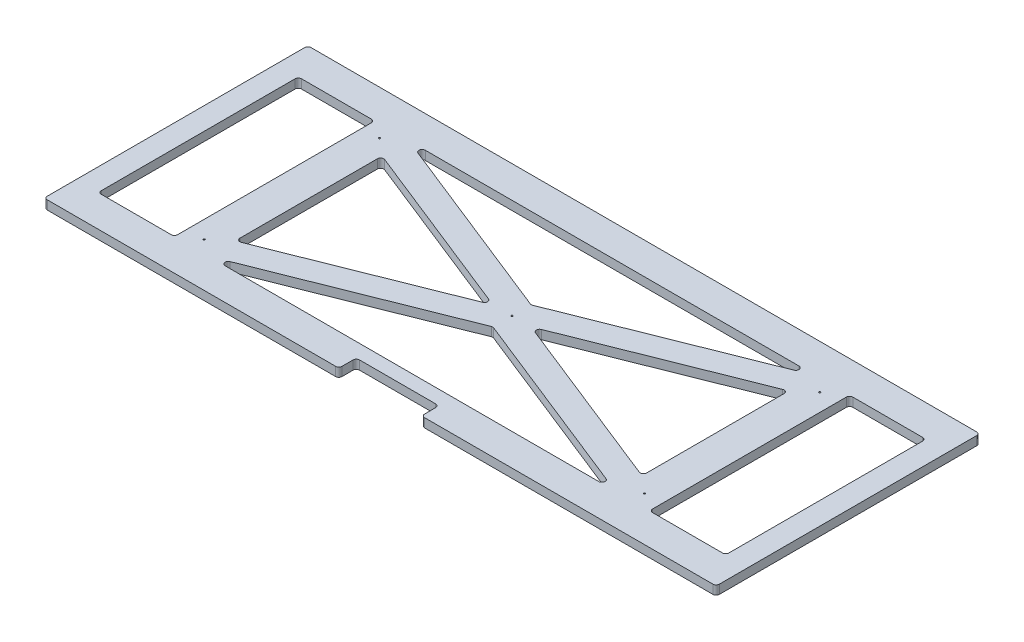
SolidWorks part; units mm, degrees
ref_plane "Front Plane" through (0, 0, 0) normal (0, 0, 1) x (1, 0, 0)
ref_plane "Top Plane" through (0, 0, 0) normal (0, 1, 0) x (1, 0, 0)
ref_plane "Right Plane" through (0, 0, 0) normal (1, 0, 0) x (0, 0, -1)
sketch "Sketch1" plane through (0, 0, 0) normal (0, 1, 0) x (1, 0, 0)
  line L1 (-671.5125, 263.525) -> (671.5125, 263.525)
  line L2 (-671.5125, 263.525) -> (-671.5125, -263.525)
  line L3 (-671.5125, -263.525) -> (671.5125, -263.525)
  line L4 (671.5125, 263.525) -> (671.5125, -263.525)
  line L5 (-671.5125, 263.525) -> (671.5125, -263.525) construction
  line L6 (-671.5125, -263.525) -> (671.5125, 263.525) construction
  point P0 (0, 0)
  dimension "D1" = 527.05
  dimension "D2" = 1343.025
extrude "Boss-Extrude1" add sketch "Sketch1" along normal blind 17.78
fillet "Fillet1" radius 6.35 4 edges at (-671.5125, 8.89, 263.525) (-671.5125, 8.89, -263.525) (671.5125, 8.89, -263.525) (671.5125, 8.89, 263.525)
hole_wizard "1/8 (0.125) Diameter Hole1" [suppressed] positions "Sketch3" profile "Sketch4" hole size "1/8" standard "ANSI Inch"
sketch "Sketch3" plane through (0, 17.78, 0) normal (0, 1, 0) x (1, 0, 0)
  line L1 (-457.2, -152.4) -> (457.2, -152.4) construction
  line L2 (-457.2, -152.4) -> (-457.2, 152.4) construction
  line L3 (-457.2, 152.4) -> (457.2, 152.4) construction
  line L4 (457.2, -152.4) -> (457.2, 152.4) construction
  line L5 (-457.2, -152.4) -> (457.2, 152.4) construction
  line L6 (-457.2, 152.4) -> (457.2, -152.4) construction
  point P0 (0, 0)
  point P1 (457.2, 152.4)
  point P32 (-457.2, -152.4)
  point P33 (-457.2, 152.4)
  point P34 (457.2, -152.4)
  dimension "D1" = 914.4
  dimension "D2" = 304.8
sketch "Sketch4" plane through (0, 17.78, 0) normal (1, 0, 0) x (0, 0, 1)
  line L0 (0, 0) -> (0, 17.78)
  line L1 (0, 17.78) -> (1.5875, 17.78)
  line L2 (1.5875, 17.78) -> (1.5875, 0)
  line L5 (1.5875, 0) -> (0, 0)
  line L11 (0, -6.35) -> (0, 107.95) construction
  dimension "Thru Hole Dia." = 3.175
  dimension "Thru Hole Depth" = 17.78
sketch "Sketch2" plane through (0, 17.78, 0) normal (0, 1, 0) x (1, 0, 0)
  line L1 (-635, -330.2) -> (635, -330.2)
  line L2 (-635, -330.2) -> (-635, 330.2)
  line L3 (-635, 330.2) -> (635, 330.2)
  line L4 (635, -330.2) -> (635, 330.2)
  line L5 (-635, -330.2) -> (635, 330.2) construction
  line L6 (-635, 330.2) -> (635, -330.2) construction
  point P0 (0, 0)
  dimension "D1" = 660.4
  dimension "D2" = 1270
extrude "Boss-Extrude2" [suppressed] add sketch "Sketch2" along normal blind 9.525
sketch "Sketch5" plane through (0, 17.78, 0) normal (0, 1, 0) x (1, 0, 0)
  line L0 (-406.4, 200.025) -> (406.4, 200.025)
  line L1 (665.1625, 263.525) -> (-665.1625, 263.525) construction
  line L2 (0, 38.1) -> (-406.4, 200.025)
  line L3 (406.4, 200.025) -> (0, 38.1)
  line L4 (0, 263.525) -> (0, -263.525) construction
  line L5 (-665.1625, -263.525) -> (665.1625, -263.525) construction
  line L6 (-671.5125, 0) -> (671.5125, 0) construction
  line L7 (-671.5125, 257.175) -> (-671.5125, -257.175) construction
  line L8 (671.5125, -257.175) -> (671.5125, 257.175) construction
  line L9 (0, -38.1) -> (-406.4, -200.025)
  line L10 (-406.4, -200.025) -> (406.4, -200.025)
  line L11 (406.4, -200.025) -> (0, -38.1)
  line L12 (406.4, 146.7445) -> (406.4, -146.7445)
  line L13 (406.4, -146.7445) -> (38.1, 0)
  line L14 (406.4, 146.7445) -> (38.1, 0)
  line L15 (-406.4, 146.7445) -> (-38.1, 0)
  line L16 (-406.4, 146.7445) -> (-406.4, -146.7445)
  line L17 (-406.4, -146.7445) -> (-38.1, 0)
  line L18 (627.0625, -200.025) -> (474.6625, -200.025)
  line L19 (-627.0625, -200.025) -> (-474.6625, -200.025)
  line L20 (-627.0625, -200.025) -> (-627.0625, 200.025)
  line L21 (-627.0625, 200.025) -> (-474.6625, 200.025)
  line L22 (-474.6625, -200.025) -> (-474.6625, 200.025)
  line L23 (-627.0625, -200.025) -> (-474.6625, 200.025) construction
  line L24 (-627.0625, 200.025) -> (-474.6625, -200.025) construction
  line L25 (627.0625, -200.025) -> (627.0625, 200.025)
  line L26 (627.0625, 200.025) -> (474.6625, 200.025)
  line L27 (474.6625, -200.025) -> (474.6625, 200.025)
  circle A0 centre (0, 0) radius 38.1 construction
  point P3 (0, 200.025)
  point P30 (-550.8625, 0)
  dimension "D2" = 76.2
  dimension "D4" = 152.4
  dimension "D1" = 63.5
  dimension "D3" = 812.8
  dimension "D5" = 44.45
extrude "Cut-Extrude1" cut sketch "Sketch5" against normal through all
hole_wizard "1/8 (0.125) Diameter Hole2" positions "Sketch6" profile "Sketch7" hole size "1/8" standard "ANSI Inch" end condition through all
sketch "Sketch6" plane through (0, 17.78, 0) normal (0, 1, 0) x (1, 0, 0)
  line L1 (439.8656, 175.259) -> (-439.8656, 175.259) construction
  line L2 (439.8656, 175.259) -> (439.8656, -175.259) construction
  line L3 (439.8656, -175.259) -> (-439.8656, -175.259) construction
  line L4 (-439.8656, 175.259) -> (-439.8656, -175.259) construction
  line L5 (439.8656, 175.259) -> (-439.8656, -175.259) construction
  line L6 (439.8656, -175.259) -> (-439.8656, 175.259) construction
  line L7 (38.1, 0) -> (406.4, -146.7445) construction
  point P1 (0, 0)
  point P2 (-439.8656, -175.259)
  point P165 (439.8656, 175.259)
  point P166 (439.8656, -175.259)
  point P167 (-439.8656, 175.259)
  point P179 (0, 0)
sketch "Sketch7" plane through (0, 17.78, 0) normal (1, 0, 0) x (0, 0, 1)
  line L0 (0, 0) -> (0, 17.78)
  line L1 (0, 17.78) -> (1.5875, 17.78)
  line L2 (1.5875, 17.78) -> (1.5875, 0)
  line L5 (1.5875, 0) -> (0, 0)
  line L11 (0, -6.35) -> (0, 107.95) construction
  dimension "Thru Hole Dia." = 3.175
  dimension "Thru Hole Depth" = 17.78
sketch "Sketch8" plane through (0, 17.78, 0) normal (0, 1, 0) x (1, 0, 0)
  line L0 (-665.1625, -263.525) -> (665.1625, -263.525) construction
  line L2 (-82.55, -263.525) -> (-82.55, -234.95)
  line L3 (-76.2, -228.6) -> (76.2, -228.6)
  line L4 (82.55, -263.525) -> (82.55, -234.95)
  line L5 (0, -263.525) -> (82.55, -228.6) construction
  line L6 (-82.55, -228.6) -> (0, -263.525) construction
  line L7 (-82.55, -263.525) -> (82.55, -263.525)
  arc A0 (76.2, -228.6) -> (82.55, -234.95) centre (76.2, -234.95) cw
  arc A1 (-82.55, -234.95) -> (-76.2, -228.6) centre (-76.2, -234.95) cw
  point P0 (0, -263.525)
  dimension "D1" = 6.35
extrude "Cut-Extrude2" cut sketch "Sketch8" against normal through all
fillet "Fillet2" radius 6.35 22 edges at (474.6625, 8.89, -200.025) (474.6625, 8.89, 200.025) (627.0625, 8.89, 200.025) (406.4, 8.89, 146.7445) (406.4, 8.89, 200.025) (627.0625, 8.89, -200.025) (406.4, 8.89, -146.7445) (406.4, 8.89, -200.025) (38.1, 8.89, 0) (0, 8.89, 38.1) (0, 8.89, -38.1) (-38.1, 8.89, 0) (-406.4, 8.89, 200.025) (-406.4, 8.89, -200.025) (-406.4, 8.89, -146.7445) (-406.4, 8.89, 146.7445) (-627.0625, 8.89, 200.025) (-474.6625, 8.89, 200.025) (-474.6625, 8.89, -200.025) (-627.0625, 8.89, -200.025) (-82.55, 8.89, 263.525) (82.55, 8.89, 263.525)
